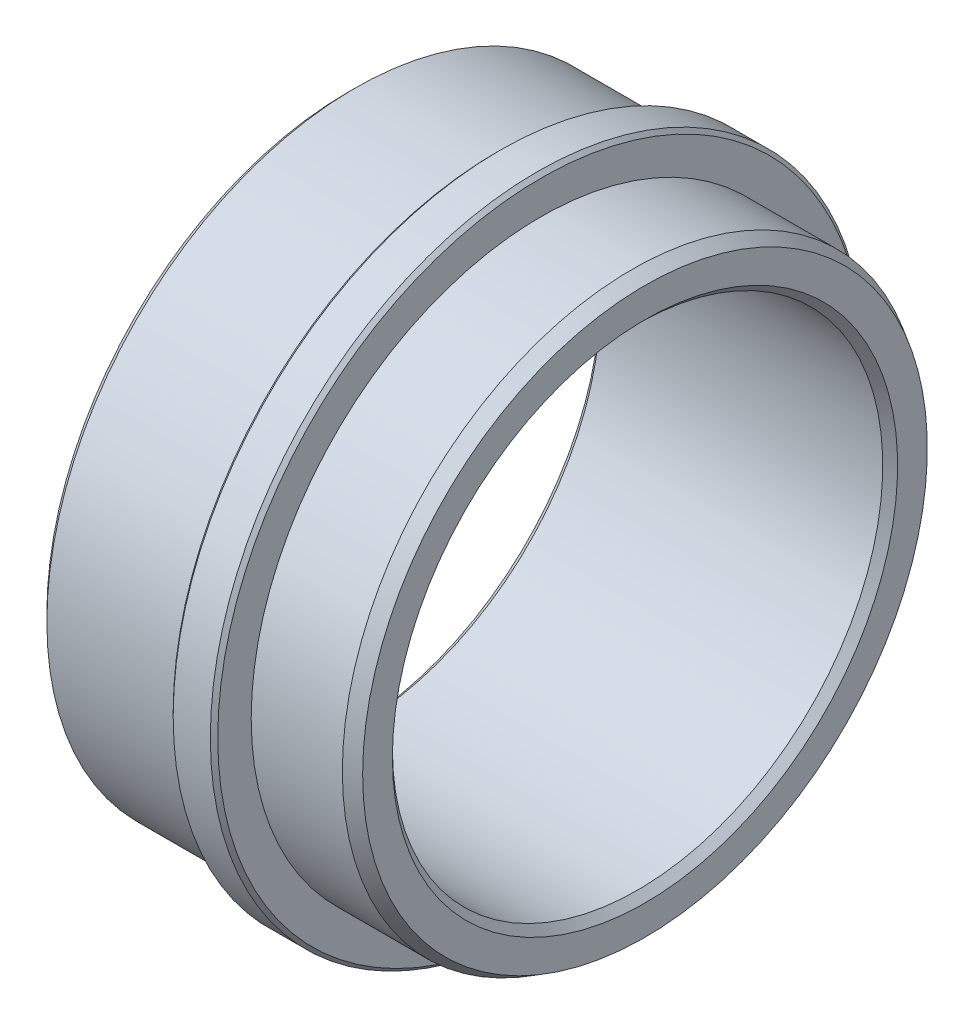
SolidWorks part; units mm, degrees
ref_plane "Plan de face" through (0, 0, 0) normal (0, 0, 1) x (1, 0, 0)
ref_plane "Plan de dessus" through (0, 0, 0) normal (0, 1, 0) x (1, 0, 0)
ref_plane "Plan de droite" through (0, 0, 0) normal (1, 0, 0) x (0, 0, -1)
sketch "Esquisse1" plane through (0, 0, 0) normal (0, 0, 1) x (1, 0, 0)
  line L0 (-13.9411, 17) -> (-13.9411, 20.25)
  line L1 (-13.4411, 20.75) -> (-3.9411, 20.75)
  line L2 (-3.9411, 20.75) -> (-3.9411, 21.75)
  line L3 (-3.6911, 22) -> (-1.1911, 22)
  line L4 (-0.9411, 21.75) -> (-0.9411, 19.5)
  line L5 (-0.9411, 19.5) -> (5.1929, 19.5)
  line L6 (6.0589, 19) -> (6.0589, 17)
  line L7 (5.5589, 16.5) -> (-13.4411, 16.5)
  line L8 (0, 0) -> (53.3274, 0) construction
  line L9 (-13.9411, 20.25) -> (-13.4411, 20.75)
  line L10 (-3.9411, 21.75) -> (-3.6911, 22)
  line L11 (-1.1911, 22) -> (-0.9411, 21.75)
  line L12 (5.1929, 19.5) -> (6.0589, 19)
  line L13 (6.0589, 17) -> (5.5589, 16.5)
  line L14 (-13.4411, 16.5) -> (-13.9411, 17)
  point P0 (-13.9411, 16.5)
  point P1 (-13.9411, 20.75)
  point P3 (6.0589, 16.5)
  point P4 (-3.9411, 22)
  point P5 (-0.9411, 22)
  point P7 (6.0589, 19.5)
  dimension "D1" = 19.5
  dimension "D2" = 20.75
  dimension "D3" = 3
  dimension "D4" = 7
  dimension "D5" = 10
  dimension "D6" = 3
  dimension "D7" = 0.5
  dimension "D8" = 45
  dimension "D9" = 0.25
  dimension "D10" = 45
  dimension "D11" = 0.25
  dimension "D12" = 45
  dimension "D13" = 0.5
  dimension "D14" = 60
  dimension "D15" = 0.5
  dimension "D16" = 45
  dimension "D17" = 0.5
  dimension "D18" = 45
  dimension "D19" = 22
revolve "Révolution1" add sketch "Esquisse1" angle 360 about L8
